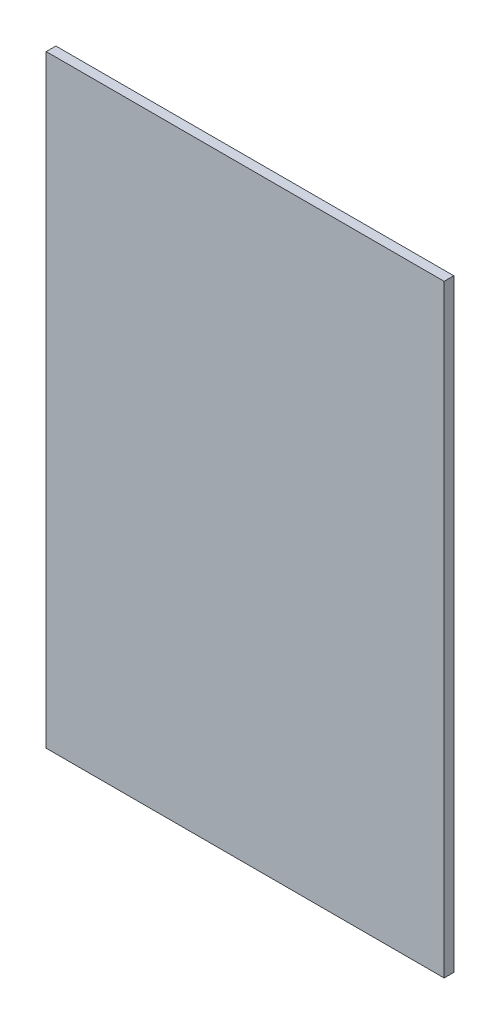
SolidWorks part; units mm, degrees
material "Acrylic (Medium-high impact)"
ref_plane "Front Plane" through (0, 0, 0) normal (0, 0, 1) x (1, 0, 0)
ref_plane "Top Plane" through (0, 0, 0) normal (0, 1, 0) x (1, 0, 0)
ref_plane "Right Plane" through (0, 0, 0) normal (1, 0, 0) x (0, 0, -1)
sketch "Sketch1" plane through (0, 0, 0) normal (0, 0, 1) x (1, 0, 0)
  line L1 (2.032, 2.032) -> (85.796, 2.032)
  line L2 (2.032, 2.032) -> (2.032, 129.032)
  line L3 (2.032, 129.032) -> (85.796, 129.032)
  line L4 (85.796, 2.032) -> (85.796, 129.032)
extrude "Boss-Extrude1" add sketch "Sketch1" against normal blind 2.032
